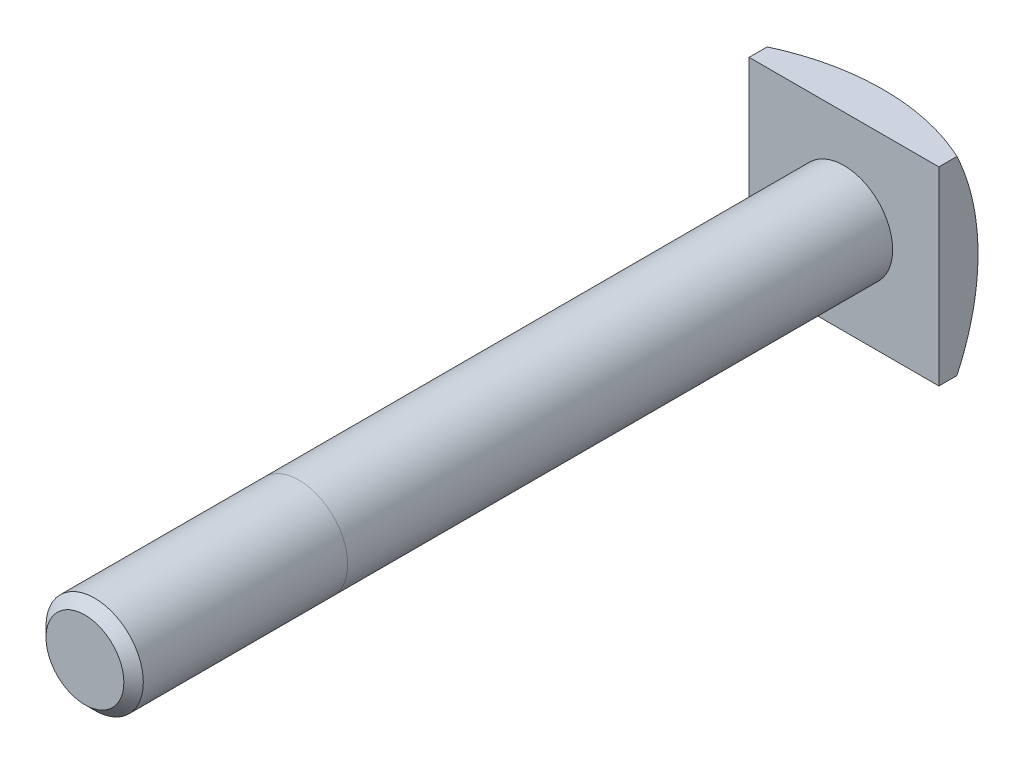
SolidWorks part; units mm, degrees
ref_plane "Front Plane" through (0, 0, 0) normal (0, 0, 1) x (1, 0, 0)
ref_plane "Top Plane" through (0, 0, 0) normal (0, 1, 0) x (1, 0, 0)
ref_plane "Right Plane" through (0, 0, 0) normal (1, 0, 0) x (0, 0, -1)
sketch "Sketch2" plane through (0, 0, 0) normal (0, 0, 1) x (1, 0, 0)
  line L1 (-9.75, 9.75) -> (9.75, 9.75)
  line L2 (-9.75, 9.75) -> (-9.75, -9.75)
  line L3 (-9.75, -9.75) -> (9.75, -9.75)
  line L4 (9.75, 9.75) -> (9.75, -9.75)
  line L5 (-9.75, 9.75) -> (9.75, -9.75) construction
  line L6 (-9.75, -9.75) -> (9.75, 9.75) construction
  point P0 (0, 0)
extrude "Boss-Extrude1" add sketch "Sketch2" along normal blind 6
sketch "Sketch3" plane through (0, 0, 6) normal (0, 0, 1) x (1, 0, 0)
  circle A0 centre (0, 0) radius 5
extrude "Boss-Extrude2" add sketch "Sketch3" along normal blind 78
chamfer "Chamfer1" distance 1 angle 45 1 edges at (5, 0, 84)
sketch "Sketch4" plane through (0, 0, 0) normal (0, 1, 0) x (1, 0, 0)
  line L0 (0, 0) -> (0, -25) construction
  line L1 (0, -25) -> (33.673, -25) construction
  line L2 (0, -25) -> (0, 8.673) construction
  line L3 (0, 8.673) -> (0, 0)
  line L4 (33.673, -25) -> (25, -25)
  arc A2 (25, -25) -> (0, 0) centre (0, -25) ccw
  arc A3 (33.673, -25) -> (0, 8.673) centre (0, -25) ccw
  dimension "D1" = 50
revolve "Cut-Revolve1" cut sketch "Sketch4" angle 360 about L0
sketch "Sketch5" plane through (0, 0, 0) normal (0, 1, 0) x (1, 0, 0)
  line L0 (-5, -62) -> (5, -62)
  line L1 (5, -83) -> (5, -6) construction
  line L2 (-4, -84) -> (4, -84) construction
  line L3 (-5, -6) -> (-5, -83) construction
  point P6 (0, 0)
  dimension "D1" = 22
split line "Split Line3"
